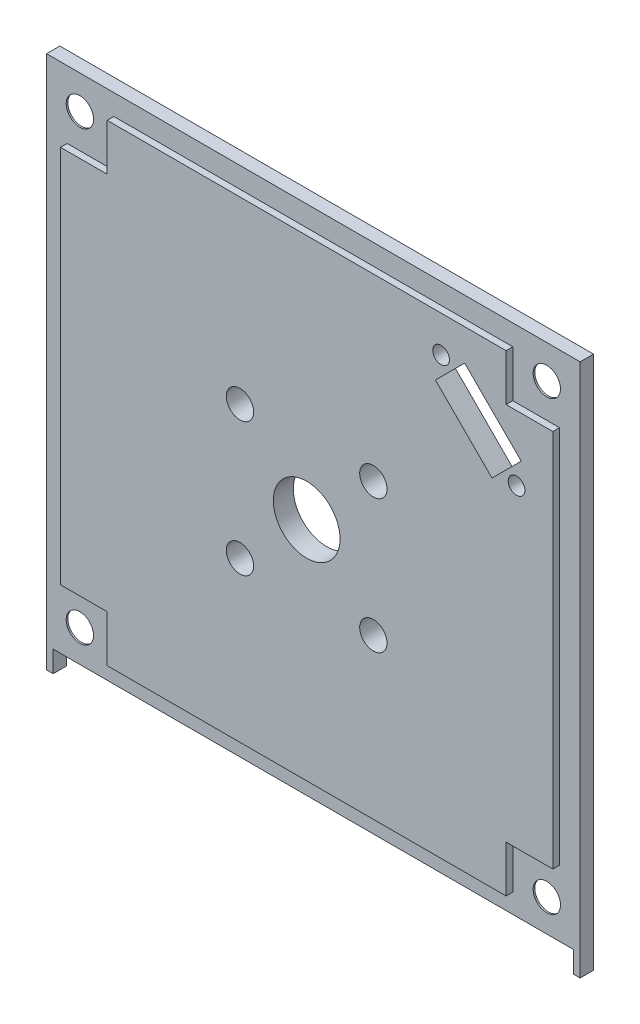
SolidWorks part; units mm, degrees
ref_plane "Plan de face" through (0, 0, 0) normal (0, 0, 1) x (1, 0, 0)
ref_plane "Plan de dessus" through (0, 0, 0) normal (0, 1, 0) x (1, 0, 0)
ref_plane "Plan de droite" through (0, 0, 0) normal (1, 0, 0) x (0, 0, -1)
sketch "Esquisse1" plane through (0, 0, 0) normal (0, 0, 1) x (1, 0, 0)
  line L1 (0, 0) -> (80, 0)
  line L2 (0, 0) -> (0, 80)
  line L3 (0, 80) -> (80, 80)
  line L4 (80, 0) -> (80, 80)
  dimension "D1" = 80
  dimension "D2" = 80
extrude "Boss.-Extru.1" add sketch "Esquisse1" along normal blind 2
sketch "Esquisse2" plane through (0, 0, 2) normal (0, 0, 1) x (1, 0, 0)
  line L0 (10.1, 6.1) -> (10.1, 13.1)
  line L1 (10.1, 13.1) -> (3.1, 13.1)
  line L2 (3.1, 13.1) -> (3.1, 69.9)
  line L3 (3.1, 69.9) -> (10.1, 69.9)
  line L4 (10.1, 69.9) -> (10.1, 76.9)
  line L5 (10.1, 76.9) -> (69.9, 76.9)
  line L6 (69.9, 76.9) -> (69.9, 69.9)
  line L7 (69.9, 69.9) -> (76.9, 69.9)
  line L8 (76.9, 69.9) -> (76.9, 13.1)
  line L9 (76.9, 13.1) -> (69.9, 13.1)
  line L10 (69.9, 13.1) -> (69.9, 6.1)
  line L11 (69.9, 6.1) -> (10.1, 6.1)
  line L12 (0, 80) -> (0, 0) construction
  line L13 (80, 0) -> (80, 80) construction
  line L14 (80, 80) -> (0, 80) construction
  line L15 (0, 0) -> (80, 0) construction
  point P16 (40, 80)
  dimension "D1" = 3.1
  dimension "D2" = 3.1
  dimension "D3" = 3.1
  dimension "D4" = 7
  dimension "D5" = 10.1
  dimension "D6" = 13.1
  dimension "D7" = 13.1
  dimension "D8" = 10.1
  dimension "D9" = 10.1
  dimension "D10" = 10.1
  dimension "D11" = 10.1
  dimension "D12" = 10.1
extrude "Boss.-Extru.2" add sketch "Esquisse2" along normal blind 1
sketch "Esquisse3" plane through (0, 0, 2) normal (0, 0, 1) x (1, 0, 0)
  line L0 (0, 80) -> (0, 0) construction
  line L1 (80, 0) -> (80, 80) construction
  line L2 (80, 80) -> (0, 80) construction
  line L3 (0, 0) -> (80, 0) construction
  line L5 (1, 0) -> (79, 0)
  line L6 (1, 0) -> (1, 3.2)
  line L7 (1, 3.2) -> (79, 3.2)
  line L8 (79, 0) -> (79, 3.2)
  circle A0 centre (5, 75) radius 2.05
  circle A1 centre (75, 75) radius 2.05
  circle A2 centre (75, 8) radius 2.05
  circle A3 centre (5, 8) radius 2.05
  dimension "D1" = 4.1
  dimension "D2" = 4.1
  dimension "D3" = 4.1
  dimension "D4" = 4.1
  dimension "D5" = 5
  dimension "D6" = 5
  dimension "D7" = 5
  dimension "D8" = 5
  dimension "D9" = 5
  dimension "D10" = 5
  dimension "D11" = 8
  dimension "D12" = 8
  dimension "D13" = 3.2
  dimension "D14" = 1
  dimension "D15" = 1
extrude "Enlèv. mat.-Extru.1" cut sketch "Esquisse3" against normal through all
sketch "Esquisse4" plane through (0, 0, 3) normal (0, 0, 1) x (1, 0, 0)
  line L0 (80, 80) -> (0, 80) construction
  line L1 (0, 80) -> (0, 0) construction
  line L2 (80, 0) -> (80, 80) construction
  circle A0 centre (40, 40) radius 5
  circle A1 centre (30, 50) radius 2.05
  circle A2 centre (30, 30) radius 2.05
  circle A3 centre (50, 30) radius 2.05
  circle A4 centre (50, 50) radius 2.05
  dimension "D1" = 4.1
  dimension "D2" = 4.1
  dimension "D3" = 4.1
  dimension "D4" = 4.1
  dimension "D5" = 10
  dimension "D6" = 40
  dimension "D7" = 40
  dimension "D8" = 30
  dimension "D9" = 30
  dimension "D10" = 30
  dimension "D11" = 30
  dimension "D12" = 30
  dimension "D13" = 30
  dimension "D14" = 30
  dimension "D15" = 30
extrude "Enlèv. mat.-Extru.2" cut sketch "Esquisse4" against normal through all
chamfer "Chanfrein1" distance 1.75 angle 56 4 edges at (77.05, 8, 0) (7.05, 8, 0) (7.05, 75, 0) (77.05, 75, 0)
sketch "Esquisse6" plane through (0, 0, 0) normal (0, 0, -1) x (-1, 0, 0)
  line L0 (-70.6159, 56.4738) -> (-56.4738, 70.6159)
  line L1 (-56.4738, 70.6159) -> (-60.8579, 75)
  line L2 (-60.8579, 75) -> (-75, 60.8579)
  line L3 (-75, 60.8579) -> (-70.6159, 56.4738)
  line L5 (-80, 80) -> (0, 80) construction
  line L7 (-80, 0) -> (-80, 80) construction
  dimension "D1" = 90
  dimension "D2" = 20
  dimension "D3" = 6.2
  dimension "D4" = 45
  dimension "D5" = 5
  dimension "D9" = 5
extrude "Enlèv. mat.-Extru.3" cut sketch "Esquisse6" against normal blind 1
sketch "Esquisse8" plane through (0, 0, 1) normal (0, 0, -1) x (-1, 0, 0)
  line L0 (-67.7875, 59.3022) -> (-72.1716, 63.6863)
  line L1 (-70.6159, 56.4738) -> (-56.4738, 70.6159) construction
  line L2 (-60.8579, 75) -> (-75, 60.8579) construction
  line L3 (-72.1716, 63.6863) -> (-63.6863, 72.1716)
  line L4 (-60.8579, 75) -> (-75, 60.8579) construction
  line L5 (-63.6863, 72.1716) -> (-59.3022, 67.7875)
  line L6 (-59.3022, 67.7875) -> (-67.7875, 59.3022)
  line L7 (-56.4738, 70.6159) -> (-60.8579, 75) construction
  line L8 (-75, 60.8579) -> (-70.6159, 56.4738) construction
  line L9 (-56.4738, 70.6159) -> (-60.8579, 75) construction
  circle A0 centre (-60.1508, 71.4645) radius 1.25
  circle A1 centre (-71.4645, 60.1508) radius 1.25
  dimension "D3" = 2.5
  dimension "D4" = 2.5
  dimension "D1" = 12
  dimension "D2" = 4
  dimension "D5" = 3
  dimension "D6" = 3
  dimension "D7" = 2
  dimension "D8" = 2
extrude "Enlèv. mat.-Extru.4" cut sketch "Esquisse8" against normal through all
